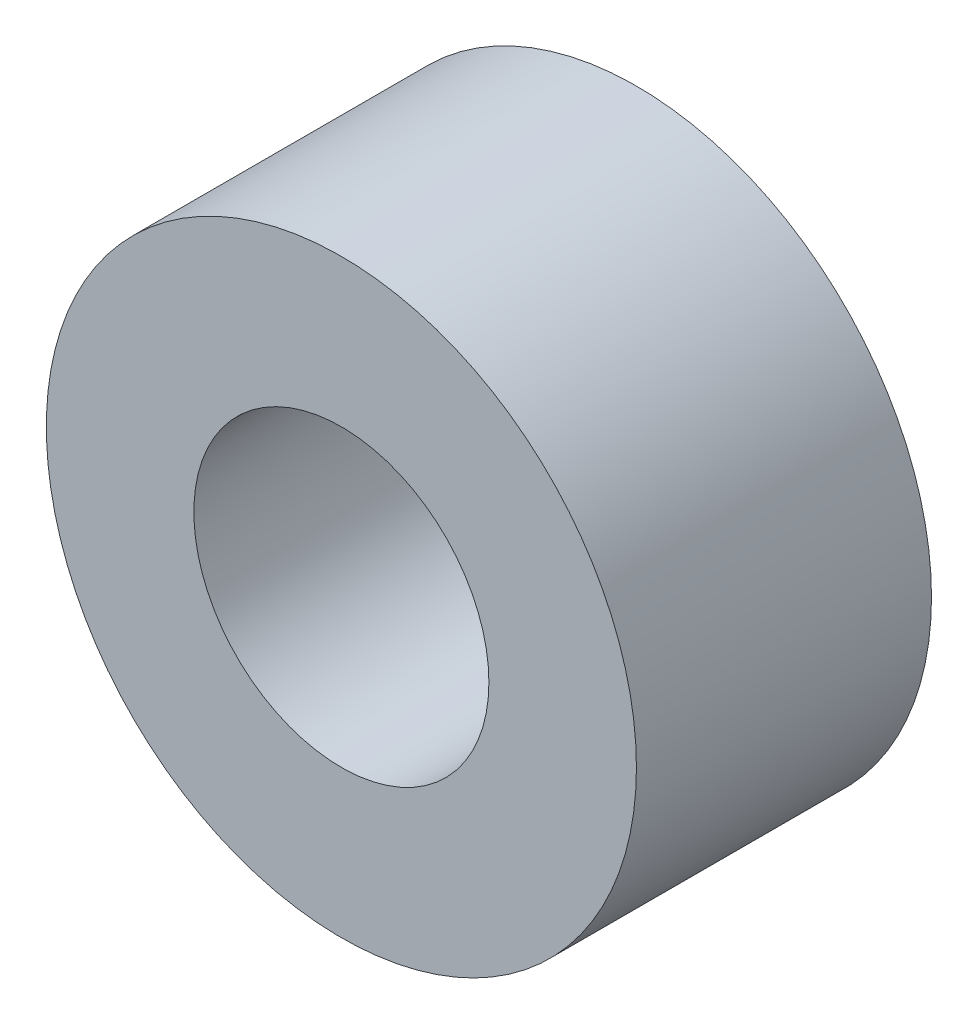
SolidWorks part; units mm, degrees
ref_plane "前视基准面" through (0, 0, 0) normal (0, 0, 1) x (1, 0, 0)
ref_plane "上视基准面" through (0, 0, 0) normal (0, 1, 0) x (1, 0, 0)
ref_plane "右视基准面" through (0, 0, 0) normal (1, 0, 0) x (0, 0, -1)
sketch "草图1" plane through (0, 0, 0) normal (0, 0, 1) x (1, 0, 0)
  circle A0 centre (0, 0) radius 1.5
  circle A1 centre (0, 0) radius 3
extrude "凸台-拉伸1" add sketch "草图1" along normal blind 3
